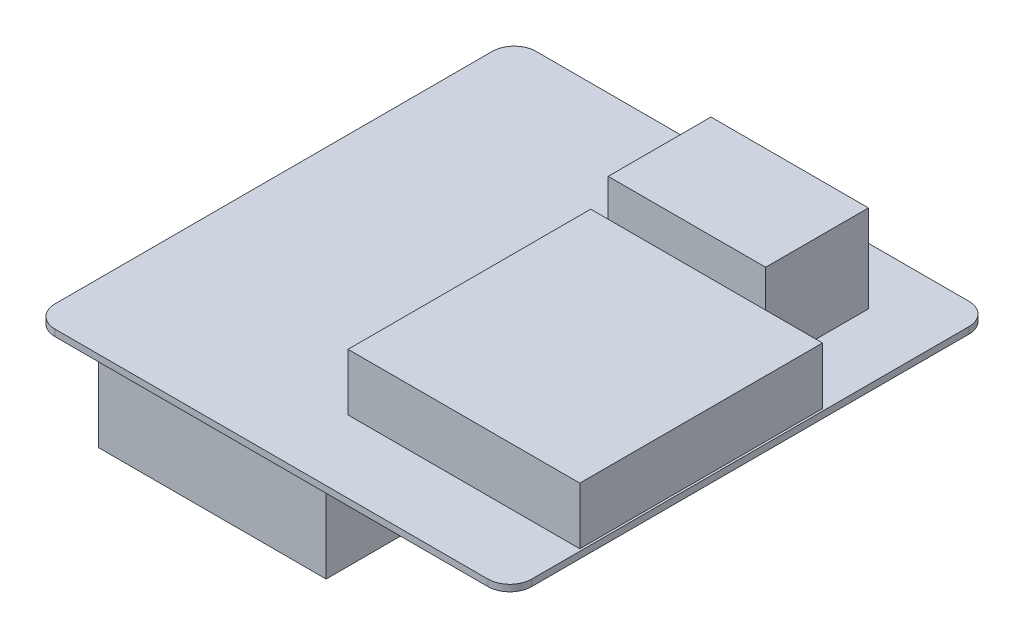
SolidWorks part; units mm, degrees
ref_plane "Plan de face" through (0, 0, 0) normal (0, 0, 1) x (1, 0, 0)
ref_plane "Plan de dessus" through (0, 0, 0) normal (0, 1, 0) x (1, 0, 0)
ref_plane "Plan de droite" through (0, 0, 0) normal (1, 0, 0) x (0, 0, -1)
sketch "Esquisse1" plane through (0, 0, 0) normal (0, 1, 0) x (1, 0, 0)
  line L1 (0, 0) -> (109, 0)
  line L2 (0, 0) -> (0, 110)
  line L3 (0, 110) -> (109, 110)
  line L4 (109, 0) -> (109, 110)
  dimension "D1" = 110
  dimension "D2" = 109
extrude "Boss.-Extru.1" add sketch "Esquisse1" along normal blind 1.5
fillet "Congé1" radius 5 4 edges at (109, 0.75, 0) (109, 0.75, -110) (0, 0.75, -110) (0, 0.75, 0)
sketch "Esquisse2" plane through (0, 0, 0) normal (0, -1, 0) x (1, 0, 0)
  line L0 (0, -105) -> (0, -5) construction
  line L1 (3, -12) -> (55, -12)
  line L2 (3, -12) -> (3, -97.5)
  line L3 (3, -97.5) -> (55, -97.5)
  line L4 (55, -12) -> (55, -97.5)
  line L5 (5, 0) -> (104, 0) construction
  line L6 (109, -5) -> (109, -105) construction
  line L7 (104, -110) -> (5, -110) construction
  dimension "D1" = 3
  dimension "D2" = 12
  dimension "D3" = 54
  dimension "D4" = 12.5
extrude "Boss.-Extru.2" add sketch "Esquisse2" along normal blind 29
sketch "Esquisse3" plane through (0, 1.5, 0) normal (0, 1, 0) x (1, 0, 0)
  line L0 (109, 5) -> (109, 105) construction
  line L1 (57, 18) -> (107, 18)
  line L2 (57, 18) -> (57, 67)
  line L3 (57, 67) -> (107, 67)
  line L4 (107, 18) -> (107, 67)
  line L5 (5, 0) -> (104, 0) construction
  line L6 (104, 110) -> (5, 110) construction
  line L7 (0, 105) -> (0, 5) construction
  line L9 (55.5, 16.5) -> (108.5, 16.5)
  line L10 (55.5, 16.5) -> (55.5, 72)
  line L11 (55.5, 72) -> (108.5, 72)
  line L12 (108.5, 16.5) -> (108.5, 72)
  dimension "D1" = 2
  dimension "D2" = 18
  dimension "D3" = 43
  dimension "D4" = 57
  dimension "D5" = 5
  dimension "D6" = 1.5
  dimension "D7" = 1.5
  dimension "D8" = 1.5
extrude "Boss.-Extru.3" add sketch "Esquisse3" along normal blind 13
sketch "Esquisse4" plane through (0, 1.5, 0) normal (0, 1, 0) x (1, 0, 0)
  line L1 (107, 18) -> (57, 18)
  line L2 (107, 18) -> (107, 67)
  line L3 (107, 67) -> (57, 67)
  line L4 (57, 18) -> (57, 67)
extrude "Boss.-Extru.4" add sketch "Esquisse4" along normal blind 13
sketch "Esquisse5" plane through (0, 1.5, 0) normal (0, 1, 0) x (1, 0, 0)
  line L0 (104, 110) -> (5, 110) construction
  line L1 (58, 73.5) -> (94, 73.5)
  line L2 (58, 73.5) -> (58, 97)
  line L3 (58, 97) -> (94, 97)
  line L4 (94, 73.5) -> (94, 97)
  line L5 (109, 5) -> (109, 105) construction
  line L6 (5, 0) -> (104, 0) construction
  line L7 (0, 105) -> (0, 5) construction
  dimension "D1" = 13
  dimension "D2" = 15
  dimension "D3" = 73.5
  dimension "D4" = 58
extrude "Boss.-Extru.5" add sketch "Esquisse5" along normal blind 20
